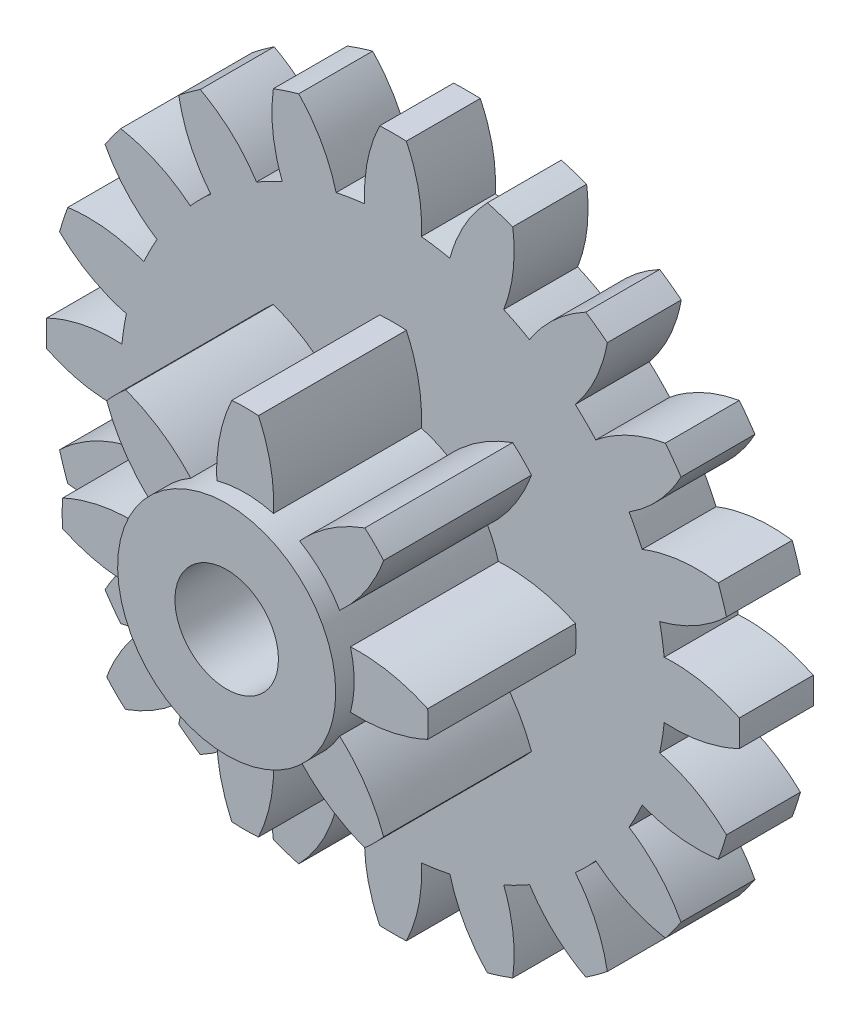
SolidWorks part; units mm, degrees
ref_plane "Front" through (0, 0, 0) normal (0, 0, 1) x (1, 0, 0)
ref_plane "Top" through (0, 0, 0) normal (0, 1, 0) x (1, 0, 0)
ref_plane "Right" through (0, 0, 0) normal (1, 0, 0) x (0, 0, -1)
sketch "草图1" plane through (0, 0, 0) normal (0, 0, 1) x (1, 0, 0)
  line L0 (0, 5.5081) -> (0, -0.6703) construction
  line L1 (0, 0) -> (-0.6106, 5.8096) construction
  line L2 (0, 0) -> (0.5998, 5.7068) construction
  arc A0 (-0.3826, 3.6676) -> (-0.7695, 3.6063) centre (0, 0) ccw
  arc A1 (0.18, 4.684) -> (-0.18, 4.684) centre (0, 0) ccw
  arc A3 (1.6186, 4.3992) -> (1.2763, 4.5104) centre (0, 0) ccw
  arc A4 (2.8988, 3.6837) -> (2.6076, 3.8953) centre (0, 0) ccw
  arc A5 (3.8953, 2.6076) -> (3.6837, 2.8988) centre (0, 0) ccw
  arc A6 (4.5104, 1.2763) -> (4.3992, 1.6186) centre (0, 0) ccw
  arc A7 (4.684, -0.18) -> (4.684, 0.18) centre (0, 0) ccw
  arc A8 (4.3992, -1.6186) -> (4.5104, -1.2763) centre (0, 0) ccw
  arc A9 (3.6837, -2.8988) -> (3.8953, -2.6076) centre (0, 0) ccw
  arc A10 (2.6076, -3.8953) -> (2.8988, -3.6837) centre (0, 0) ccw
  arc A11 (1.2763, -4.5104) -> (1.6186, -4.3992) centre (0, 0) ccw
  arc A12 (-0.18, -4.684) -> (0.18, -4.684) centre (0, 0) ccw
  arc A13 (-1.6186, -4.3992) -> (-1.2763, -4.5104) centre (0, 0) ccw
  arc A14 (-2.8988, -3.6837) -> (-2.6076, -3.8953) centre (0, 0) ccw
  arc A15 (-3.8953, -2.6076) -> (-3.6837, -2.8988) centre (0, 0) ccw
  arc A16 (-4.5104, -1.2763) -> (-4.3992, -1.6186) centre (0, 0) ccw
  arc A17 (-4.684, 0.18) -> (-4.684, -0.18) centre (0, 0) ccw
  arc A18 (-4.3992, 1.6186) -> (-4.5104, 1.2763) centre (0, 0) ccw
  arc A19 (-3.6837, 2.8988) -> (-3.8953, 2.6076) centre (0, 0) ccw
  arc A20 (-2.6076, 3.8953) -> (-2.8988, 3.6837) centre (0, 0) ccw
  arc A21 (-1.2763, 4.5104) -> (-1.6186, 4.3992) centre (0, 0) ccw
  arc A22 (0.7695, 3.6063) -> (0.3826, 3.6676) centre (0, 0) ccw
  arc A23 (1.8462, 3.192) -> (1.4972, 3.3699) centre (0, 0) ccw
  arc A24 (2.7422, 2.4653) -> (2.4653, 2.7422) centre (0, 0) ccw
  arc A25 (3.3699, 1.4972) -> (3.192, 1.8462) centre (0, 0) ccw
  arc A26 (3.6676, 0.3826) -> (3.6063, 0.7695) centre (0, 0) ccw
  arc A27 (3.6063, -0.7695) -> (3.6676, -0.3826) centre (0, 0) ccw
  arc A28 (3.192, -1.8462) -> (3.3699, -1.4972) centre (0, 0) ccw
  arc A29 (2.4653, -2.7422) -> (2.7422, -2.4653) centre (0, 0) ccw
  arc A30 (1.4972, -3.3699) -> (1.8462, -3.192) centre (0, 0) ccw
  arc A31 (-1.4972, 3.3699) -> (-1.8462, 3.192) centre (0, 0) ccw
  arc A32 (-2.4653, 2.7422) -> (-2.7422, 2.4653) centre (0, 0) ccw
  arc A33 (-3.192, 1.8462) -> (-3.3699, 1.4972) centre (0, 0) ccw
  arc A34 (-3.6063, 0.7695) -> (-3.6676, 0.3826) centre (0, 0) ccw
  arc A35 (-3.6676, -0.3826) -> (-3.6063, -0.7695) centre (0, 0) ccw
  arc A36 (-3.3699, -1.4972) -> (-3.192, -1.8462) centre (0, 0) ccw
  arc A37 (-2.7422, -2.4653) -> (-2.4653, -2.7422) centre (0, 0) ccw
  arc A38 (-1.8462, -3.192) -> (-1.4972, -3.3699) centre (0, 0) ccw
  arc A39 (-0.7695, -3.6063) -> (-0.3826, -3.6676) centre (0, 0) ccw
  arc A40 (0.3826, -3.6676) -> (0.7695, -3.6063) centre (0, 0) ccw
  spline S0 degree 2 poles (0.18, 4.684) (0.4125, 4.2014) (0.3826, 3.6676) knots 0 0 0 1 1 1
  spline S1 degree 2 poles (-0.18, 4.684) (-0.4125, 4.2014) (-0.3826, 3.6676) knots 0 0 0 1 1 1
  spline S2 degree 2 poles (1.2763, 4.5104) (0.906, 4.1233) (0.7695, 3.6063) knots 0 0 0 1 1 1
  spline S3 degree 2 poles (1.6186, 4.3992) (1.6907, 3.8683) (1.4972, 3.3699) knots 0 0 0 1 1 1
  spline S4 degree 2 poles (2.6076, 3.8953) (2.1358, 3.6415) (1.8462, 3.192) knots 0 0 0 1 1 1
  spline S5 degree 2 poles (2.8988, 3.6837) (2.8033, 3.1566) (2.4653, 2.7422) knots 0 0 0 1 1 1
  spline S6 degree 2 poles (3.6837, 2.8988) (3.1566, 2.8033) (2.7422, 2.4653) knots 0 0 0 1 1 1
  spline S7 degree 2 poles (3.8953, 2.6076) (3.6415, 2.1358) (3.192, 1.8462) knots 0 0 0 1 1 1
  spline S8 degree 2 poles (4.3992, 1.6186) (3.8683, 1.6907) (3.3699, 1.4972) knots 0 0 0 1 1 1
  spline S9 degree 2 poles (4.5104, 1.2763) (4.1233, 0.906) (3.6063, 0.7695) knots 0 0 0 1 1 1
  spline S10 degree 2 poles (4.684, 0.18) (4.2014, 0.4125) (3.6676, 0.3826) knots 0 0 0 1 1 1
  spline S11 degree 2 poles (4.684, -0.18) (4.2014, -0.4125) (3.6676, -0.3826) knots 0 0 0 1 1 1
  spline S12 degree 2 poles (4.5104, -1.2763) (4.1233, -0.906) (3.6063, -0.7695) knots 0 0 0 1 1 1
  spline S13 degree 2 poles (4.3992, -1.6186) (3.8683, -1.6907) (3.3699, -1.4972) knots 0 0 0 1 1 1
  spline S14 degree 2 poles (3.8953, -2.6076) (3.6415, -2.1358) (3.192, -1.8462) knots 0 0 0 1 1 1
  spline S15 degree 2 poles (3.6837, -2.8988) (3.1566, -2.8033) (2.7422, -2.4653) knots 0 0 0 1 1 1
  spline S16 degree 2 poles (2.8988, -3.6837) (2.8033, -3.1566) (2.4653, -2.7422) knots 0 0 0 1 1 1
  spline S17 degree 2 poles (2.6076, -3.8953) (2.1358, -3.6415) (1.8462, -3.192) knots 0 0 0 1 1 1
  spline S18 degree 2 poles (1.6186, -4.3992) (1.6907, -3.8683) (1.4972, -3.3699) knots 0 0 0 1 1 1
  spline S19 degree 2 poles (1.2763, -4.5104) (0.906, -4.1233) (0.7695, -3.6063) knots 0 0 0 1 1 1
  spline S20 degree 2 poles (0.18, -4.684) (0.4125, -4.2014) (0.3826, -3.6676) knots 0 0 0 1 1 1
  spline S21 degree 2 poles (-0.18, -4.684) (-0.4125, -4.2014) (-0.3826, -3.6676) knots 0 0 0 1 1 1
  spline S22 degree 2 poles (-1.2763, -4.5104) (-0.906, -4.1233) (-0.7695, -3.6063) knots 0 0 0 1 1 1
  spline S23 degree 2 poles (-1.6186, -4.3992) (-1.6907, -3.8683) (-1.4972, -3.3699) knots 0 0 0 1 1 1
  spline S24 degree 2 poles (-2.6076, -3.8953) (-2.1358, -3.6415) (-1.8462, -3.192) knots 0 0 0 1 1 1
  spline S25 degree 2 poles (-2.8988, -3.6837) (-2.8033, -3.1566) (-2.4653, -2.7422) knots 0 0 0 1 1 1
  spline S26 degree 2 poles (-3.6837, -2.8988) (-3.1566, -2.8033) (-2.7422, -2.4653) knots 0 0 0 1 1 1
  spline S27 degree 2 poles (-3.8953, -2.6076) (-3.6415, -2.1358) (-3.192, -1.8462) knots 0 0 0 1 1 1
  spline S28 degree 2 poles (-4.3992, -1.6186) (-3.8683, -1.6907) (-3.3699, -1.4972) knots 0 0 0 1 1 1
  spline S29 degree 2 poles (-4.5104, -1.2763) (-4.1233, -0.906) (-3.6063, -0.7695) knots 0 0 0 1 1 1
  spline S30 degree 2 poles (-4.684, -0.18) (-4.2014, -0.4125) (-3.6676, -0.3826) knots 0 0 0 1 1 1
  spline S31 degree 2 poles (-4.684, 0.18) (-4.2014, 0.4125) (-3.6676, 0.3826) knots 0 0 0 1 1 1
  spline S32 degree 2 poles (-4.5104, 1.2763) (-4.1233, 0.906) (-3.6063, 0.7695) knots 0 0 0 1 1 1
  spline S33 degree 2 poles (-4.3992, 1.6186) (-3.8683, 1.6907) (-3.3699, 1.4972) knots 0 0 0 1 1 1
  spline S34 degree 2 poles (-3.8953, 2.6076) (-3.6415, 2.1358) (-3.192, 1.8462) knots 0 0 0 1 1 1
  spline S35 degree 2 poles (-3.6837, 2.8988) (-3.1566, 2.8033) (-2.7422, 2.4653) knots 0 0 0 1 1 1
  spline S36 degree 2 poles (-2.8988, 3.6837) (-2.8033, 3.1566) (-2.4653, 2.7422) knots 0 0 0 1 1 1
  spline S37 degree 2 poles (-2.6076, 3.8953) (-2.1358, 3.6415) (-1.8462, 3.192) knots 0 0 0 1 1 1
  spline S38 degree 2 poles (-1.6186, 4.3992) (-1.6907, 3.8683) (-1.4972, 3.3699) knots 0 0 0 1 1 1
  spline S39 degree 2 poles (-1.2763, 4.5104) (-0.906, 4.1233) (-0.7695, 3.6063) knots 0 0 0 1 1 1
  point P7 (0, 4.6875)
  point P10 (0, 4.1875)
  point P11 (-0.18, 4.684)
  point P12 (0.18, 4.684)
  point P13 (-0.35, 4.1728)
  point P14 (0.35, 4.1728)
  point P15 (0, 3.6875)
  point P16 (-0.3826, 3.6676)
  point P17 (0.3826, 3.6676)
  point P137 (0, 0)
  dimension "D1" = 7.375
  dimension "D2" = 0.18
  dimension "D3" = 20
  dimension "D4" = 9.375
  dimension "D5" = 0.18
  dimension "D6" = 0.35
  dimension "D7" = 0.35
extrude "凸台-拉伸1" add sketch "草图1" along normal mid plane 1
sketch "草图2" plane through (0, 0, -0.5) normal (0, 0, -1) x (-1, 0, 0)
  circle A0 centre (0, 0) radius 1.25
  dimension "D1" = 2.5
extrude "凸台-拉伸2" add sketch "草图2" along normal blind 0.25
sketch "草图3" plane through (0, 0, 0.5) normal (0, 0, 1) x (1, 0, 0)
  line L0 (0, 0) -> (0, 2.741) construction
  line L1 (0, 0) -> (0.7513, 2.804) construction
  line L2 (0, 0) -> (-0.7709, 2.8771) construction
  arc A0 (-0.3832, 1.4243) -> (-0.7362, 1.2782) centre (0, 0) ccw
  arc A3 (0.1799, 2.4685) -> (-0.18, 2.4684) centre (0, 0) ccw
  arc A4 (1.8727, 1.6183) -> (1.6182, 1.8727) centre (0, 0) ccw
  arc A5 (2.4685, -0.1799) -> (2.4684, 0.18) centre (0, 0) ccw
  arc A6 (1.6183, -1.8727) -> (1.8727, -1.6182) centre (0, 0) ccw
  arc A7 (-0.1799, -2.4685) -> (0.18, -2.4684) centre (0, 0) ccw
  arc A8 (-1.8727, -1.6183) -> (-1.6182, -1.8727) centre (0, 0) ccw
  arc A9 (-2.4685, 0.1799) -> (-2.4684, -0.18) centre (0, 0) ccw
  arc A10 (-1.6183, 1.8727) -> (-1.8727, 1.6182) centre (0, 0) ccw
  arc A11 (0.7362, 1.2782) -> (0.3833, 1.4243) centre (0, 0) ccw
  arc A12 (-1.2782, 0.7362) -> (-1.4243, 0.3833) centre (0, 0) ccw
  arc A13 (-1.4243, -0.3832) -> (-1.2782, -0.7362) centre (0, 0) ccw
  arc A14 (-0.7362, -1.2782) -> (-0.3833, -1.4243) centre (0, 0) ccw
  arc A15 (0.3832, -1.4243) -> (0.7362, -1.2782) centre (0, 0) ccw
  arc A16 (1.2782, -0.7362) -> (1.4243, -0.3833) centre (0, 0) ccw
  arc A17 (1.4243, 0.3832) -> (1.2782, 0.7362) centre (0, 0) ccw
  spline S0 degree 2 poles (-0.18, 2.4684) (-0.41, 1.9709) (-0.3832, 1.4243) knots 0 0 0 1 1 1
  spline S1 degree 2 poles (0.1799, 2.4685) (0.4101, 1.971) (0.3833, 1.4243) knots 0 0 0 1 1 1
  spline S2 degree 2 poles (1.8727, 1.6183) (1.6836, 1.1037) (1.2782, 0.7362) knots 0 0 0 1 1 1
  spline S3 degree 2 poles (1.6182, 1.8727) (1.1037, 1.6836) (0.7362, 1.2782) knots 0 0 0 1 1 1
  spline S4 degree 2 poles (2.4685, -0.1799) (1.971, -0.4101) (1.4243, -0.3833) knots 0 0 0 1 1 1
  spline S5 degree 2 poles (2.4684, 0.18) (1.9709, 0.41) (1.4243, 0.3832) knots 0 0 0 1 1 1
  spline S6 degree 2 poles (1.6183, -1.8727) (1.1037, -1.6836) (0.7362, -1.2782) knots 0 0 0 1 1 1
  spline S7 degree 2 poles (1.8727, -1.6182) (1.6836, -1.1037) (1.2782, -0.7362) knots 0 0 0 1 1 1
  spline S8 degree 2 poles (-0.1799, -2.4685) (-0.4101, -1.971) (-0.3833, -1.4243) knots 0 0 0 1 1 1
  spline S9 degree 2 poles (0.18, -2.4684) (0.41, -1.9709) (0.3832, -1.4243) knots 0 0 0 1 1 1
  spline S10 degree 2 poles (-1.8727, -1.6183) (-1.6836, -1.1037) (-1.2782, -0.7362) knots 0 0 0 1 1 1
  spline S11 degree 2 poles (-1.6182, -1.8727) (-1.1037, -1.6836) (-0.7362, -1.2782) knots 0 0 0 1 1 1
  spline S12 degree 2 poles (-2.4685, 0.1799) (-1.971, 0.4101) (-1.4243, 0.3833) knots 0 0 0 1 1 1
  spline S13 degree 2 poles (-2.4684, -0.18) (-1.9709, -0.41) (-1.4243, -0.3832) knots 0 0 0 1 1 1
  spline S14 degree 2 poles (-1.6183, 1.8727) (-1.1037, 1.6836) (-0.7362, 1.2782) knots 0 0 0 1 1 1
  spline S15 degree 2 poles (-1.8727, 1.6182) (-1.6836, 1.1037) (-1.2782, 0.7362) knots 0 0 0 1 1 1
  point P5 (0, 1.475)
  point P9 (0.3833, 1.4243)
  point P10 (-0.3832, 1.4243)
  point P11 (0, 2.475)
  point P12 (-0.18, 2.4684)
  point P13 (0.1799, 2.4685)
  point P14 (0, 1.975)
  point P15 (-0.3486, 1.944)
  point P16 (0.3486, 1.944)
  point P64 (0, 0)
  dimension "D1" = 2.95
  dimension "D2" = 8
  dimension "D4" = 0.3832
  dimension "D5" = 0.3832
  dimension "D6" = 0.18
  dimension "D7" = 0.18
  dimension "D8" = 0.35
  dimension "D9" = 0.35
extrude "凸台-拉伸3" add sketch "草图3" along normal blind 2
sketch "草图4" plane through (0, 0, 0) normal (0, 0, 1) x (1, 0, 0)
  circle A0 centre (0, 0) radius 0.7
  dimension "D1" = 1.4
extrude "切除-拉伸1" cut sketch "草图4" against normal through all both and the other way through all
sketch "草图7" plane through (0, 0, 2.5) normal (0, 0, 1) x (1, 0, 0)
  circle A0 centre (0, 0) radius 1.475
  dimension "D1" = 2.95
extrude "凸台-拉伸5" add sketch "草图7" along normal blind 0.25
sketch "草图8" plane through (0, 0, 2.75) normal (0, 0, 1) x (1, 0, 0)
  circle A0 centre (0, 0) radius 0.7
  dimension "D1" = 1.4
extrude "切除-拉伸2" cut sketch "草图8" against normal through all
